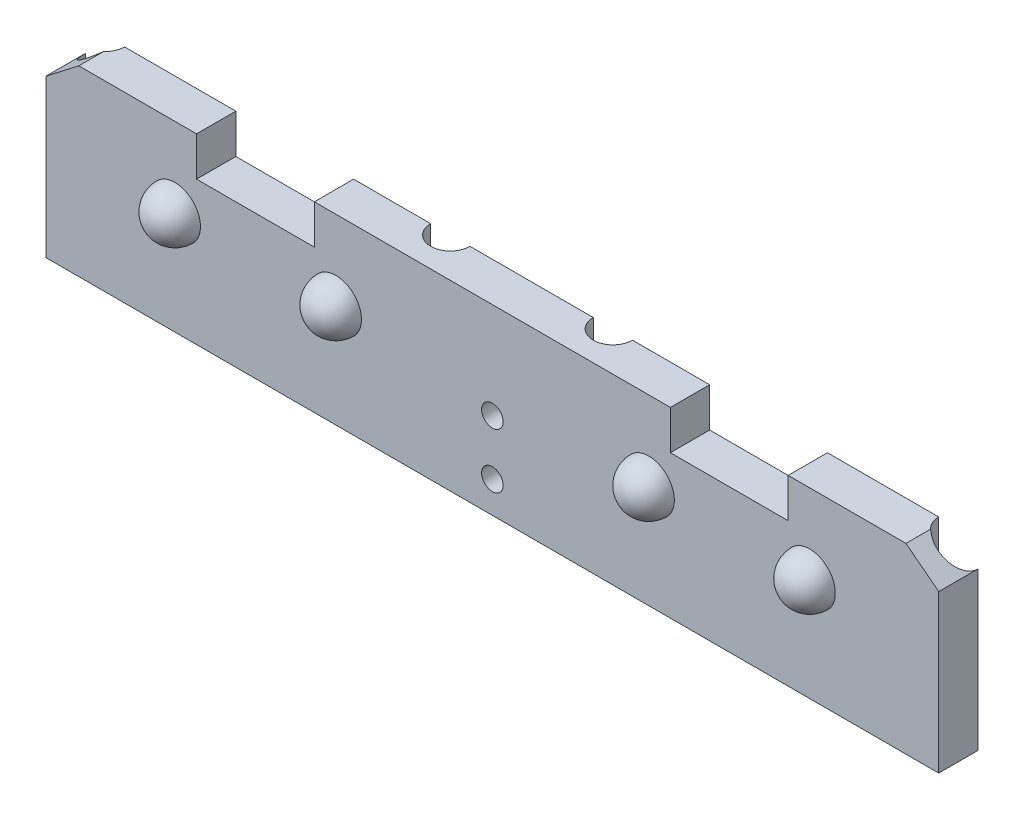
SolidWorks part; units mm, degrees
ref_plane "Front" through (0, 0, 0) normal (0, 0, 1) x (1, 0, 0)
ref_plane "Top" through (0, 0, 0) normal (0, 1, 0) x (1, 0, 0)
ref_plane "Right" through (0, 0, 0) normal (1, 0, 0) x (0, 0, -1)
sketch "Sketch1" plane through (0, 0, 0) normal (0, 0, 1) x (1, 0, 0)
  line L1 (0, 0) -> (126.7, 0)
  line L2 (0, 0) -> (0, 14)
  line L3 (0, 14) -> (126.7, 14)
  line L4 (126.7, 0) -> (126.7, 14)
  dimension "D1" = 126.7
  dimension "D2" = 14
extrude "bracketBase" add sketch "Sketch1" along normal blind 5
sketch "Sketch2" plane through (0, 0, 5) normal (0, 0, 1) x (1, 0, 0)
  line L0 (0, 0) -> (126.7, 0) construction
  line L1 (60.35, 0) -> (66.35, 0) construction
  line L2 (60.35, 0) -> (60.35, 14) construction
  line L3 (60.35, 14) -> (66.35, 14) construction
  line L4 (66.35, 0) -> (66.35, 14) construction
  line L5 (63.35, 0) -> (63.35, -7.3083) construction
  line L7 (120.7, 0) -> (126.7, 0) construction
  line L8 (120.7, 0) -> (120.7, 14) construction
  line L9 (120.7, 14) -> (126.7, 14) construction
  line L10 (126.7, 0) -> (126.7, 14) construction
  circle A0 centre (63.35, 10) radius 1.375
  circle A1 centre (63.35, 3) radius 1.375
  circle A2 centre (123.7, 10) radius 1.375
  circle A3 centre (123.7, 3) radius 1.375
  circle A4 centre (3, 3) radius 1.375
  circle A5 centre (3, 10) radius 1.375
  point P4 (63.35, 0)
  point P7 (63.35, 0)
  point P19 (63.35, 14)
  point P24 (123.7, 14)
  dimension "D3" = 2.75
  dimension "D1" = 14
  dimension "D2" = 6
  dimension "D4" = 4
  dimension "D5" = 7
extrude "mountingHoles" cut sketch "Sketch2" against normal through all both and the other way through all
sketch "distanceSensors" plane through (0, 0, 5) normal (0, 0, 1) x (1, 0, 0)
  line L0 (63.35, 0) -> (63.35, 14) construction
  line L1 (10.675, 2.25) -> (55.675, 2.25) construction
  line L2 (10.675, 2.25) -> (10.675, 22.25) construction
  line L3 (10.675, 22.25) -> (55.675, 22.25) construction
  line L4 (55.675, 2.25) -> (55.675, 22.25) construction
  line L5 (0, 0) -> (126.7, 0) construction
  line L6 (126.7, 14) -> (0, 14) construction
  line L7 (116.025, 2.25) -> (116.025, 22.25) construction
  line L8 (116.025, 2.25) -> (71.025, 2.25) construction
  line L9 (71.025, 2.25) -> (71.025, 22.25) construction
  line L10 (116.025, 22.25) -> (71.025, 22.25) construction
  circle A0 centre (63.35, 3) radius 1.375 construction
  circle A1 centre (63.35, 3) radius 1.375 construction
  circle A2 centre (19.675, 12.25) radius 9 construction
  circle A3 centre (46.675, 12.25) radius 9 construction
  circle A4 centre (80.025, 12.25) radius 9 construction
  circle A5 centre (107.025, 12.25) radius 9 construction
  point P14 (55.675, 12.25)
  dimension "D5" = 18
  dimension "D1" = 20
  dimension "D2" = 45
  dimension "D3" = 7.675
  dimension "D4" = 0.75
  dimension "D6" = 27
sketch "Sketch4" plane through (0, 0, 5) normal (0, 0, 1) x (1, 0, 0)
  line L0 (43.425, 9.0072) -> (43.425, 15.5072)
  arc A0 (43.425, 15.5072) -> (43.425, 9.0072) centre (43.425, 12.2572) ccw
  dimension "D1" = 6.5
  dimension "D2" = 0.0072
  dimension "D3" = 3.25
sketch "Sketch5" plane through (0, 0, 5) normal (0, 0, 1) x (1, 0, 0)
  line L0 (126.7, 0) -> (126.7, 14) construction
  line L1 (0, 14) -> (126.7, 14)
  line L2 (0, 14) -> (0, 22.25)
  line L3 (0, 22.25) -> (126.7, 22.25)
  line L4 (126.7, 14) -> (126.7, 22.25)
  line L5 (116.025, 22.25) -> (71.025, 22.25) construction
extrude "baseExtension" add sketch "Sketch5" against normal up to surface (5 mm away) up to face at (1.625, 3, 0)
sketch "Sketch6" plane through (0, 0, 5) normal (0, 0, 1) x (1, 0, 0)
  line L0 (33.175, 22.25) -> (33.175, 0) construction
  line L1 (10.675, 22.25) -> (55.675, 22.25) construction
  line L2 (0, 0) -> (126.7, 0) construction
  line L3 (43.425, 9.0072) -> (43.425, 15.5072) construction
  line L4 (43.425, 9.0072) -> (43.425, 15.5072) construction
  line L5 (22.925, 9.0072) -> (22.925, 15.5072)
  arc A0 (43.425, 15.5072) -> (43.425, 9.0072) centre (43.425, 12.2572) ccw construction
  arc A1 (43.425, 15.5072) -> (43.425, 9.0072) centre (43.425, 12.2572) ccw construction
  arc A2 (22.925, 15.5072) -> (22.925, 9.0072) centre (22.925, 12.2572) cw
sketch "Sketch7" plane through (0, 0, 5) normal (0, 0, 1) x (1, 0, 0)
  line L0 (43.425, 9.0072) -> (43.425, 15.5072) construction
  line L1 (43.425, 9.0072) -> (43.425, 15.5072) construction
  line L2 (63.35, 0) -> (63.35, 22.25) construction
  line L3 (126.7, 22.25) -> (0, 22.25) construction
  line L4 (83.275, 9.0072) -> (83.275, 15.5072)
  arc A0 (43.425, 15.5072) -> (43.425, 9.0072) centre (43.425, 12.2572) ccw construction
  arc A1 (43.425, 15.5072) -> (43.425, 9.0072) centre (43.425, 12.2572) ccw construction
  arc A2 (83.275, 15.5072) -> (83.275, 9.0072) centre (83.275, 12.2572) cw
sketch "Sketch8" plane through (0, 0, 5) normal (0, 0, 1) x (1, 0, 0)
  line L0 (63.35, 0) -> (63.35, 22.25) construction
  line L1 (0, 0) -> (126.7, 0) construction
  line L2 (22.925, 9.0072) -> (22.925, 15.5072) construction
  line L3 (22.925, 9.0072) -> (22.925, 15.5072) construction
  line L4 (103.775, 9.0072) -> (103.775, 15.5072)
  arc A0 (22.925, 9.0072) -> (22.925, 15.5072) centre (22.925, 12.2572) ccw construction
  arc A1 (22.925, 9.0072) -> (22.925, 15.5072) centre (22.925, 12.2572) ccw construction
  arc A2 (103.775, 9.0072) -> (103.775, 15.5072) centre (103.775, 12.2572) cw
revolve "Revolve1" add sketch "Sketch4" angle 180 about L0
revolve "Revolve2" add sketch "Sketch6" angle 180 about L5
revolve "Revolve3" add sketch "Sketch7" angle 180 about L4
revolve "Revolve4" add sketch "Sketch8" angle 180 about L4
sketch "Sketch9" plane through (0, 0, 5) normal (0, 0, 1) x (1, 0, 0)
  line L0 (10.675, 22.25) -> (55.675, 22.25) construction
  line L1 (25.675, 22.25) -> (40.675, 22.25)
  line L2 (25.675, 22.25) -> (25.675, 17.25)
  line L3 (25.675, 17.25) -> (40.675, 17.25)
  line L4 (40.675, 22.25) -> (40.675, 17.25)
  line L5 (63.35, 14) -> (63.35, 22.25) construction
  line L6 (126.7, 22.25) -> (0, 22.25) construction
  line L7 (101.025, 17.25) -> (86.025, 17.25)
  line L8 (86.025, 22.25) -> (86.025, 17.25)
  line L9 (101.025, 22.25) -> (86.025, 22.25)
  line L10 (101.025, 22.25) -> (101.025, 17.25)
  point P7 (33.175, 22.25)
  point P8 (33.175, 22.25)
  dimension "D1" = 15
  dimension "D2" = 5
extrude "Cut-Extrude2" cut sketch "Sketch9" against normal through all both and the other way through all
sketch "Sketch10" plane through (0, 0, 5) normal (0, 0, 1) x (1, 0, 0)
  line L0 (116.025, 22.25) -> (126.7, 14)
  line L3 (126.7, 14) -> (126.7, 22.25)
  line L4 (126.7, 22.25) -> (116.025, 22.25)
  line L5 (63.35, 14) -> (63.35, 22.25) construction
  line L6 (86.025, 22.25) -> (40.675, 22.25) construction
  line L7 (0, 14) -> (0, 22.25)
  line L8 (10.675, 22.25) -> (0, 14)
  line L9 (0, 22.25) -> (10.675, 22.25)
extrude "Cut-Extrude3" cut sketch "Sketch10" against normal through all both and the other way through all
sketch "Sketch11" plane through (0, 0, 0) normal (0, -1, 0) x (1, 0, 0)
  line L2 (126.7, 5) -> (126.7, 0) construction
  line L3 (63.35, 0) -> (63.35, 5) construction
  line L4 (0, 0) -> (126.7, 0) construction
  line L5 (0, 5) -> (126.7, 5) construction
  circle A1 centre (126.95, 1.1558) radius 2.5
  circle A2 centre (-0.25, 1.1558) radius 2.5
  dimension "D1" = 5
  dimension "D2" = 0.25
  dimension "D3" = 1.1825
extrude "Cut-Extrude4" cut sketch "Sketch11" against normal through all
sketch "Sketch12" plane through (0, 0, 0) normal (0, -1, 0) x (1, 0, 0)
  line L1 (1.9668, 0) -> (124.7332, 0) construction
  line L2 (63.35, 5) -> (63.35, 0) construction
  line L3 (0, 5) -> (126.7, 5) construction
  circle A0 centre (117.7, 0) radius 2.5
  circle A1 centre (73.7, 0) radius 2.5
  circle A3 centre (53, 0) radius 2.5
  circle A4 centre (9, 0) radius 2.5
  dimension "D1" = 5
  dimension "D2" = 9
  dimension "D3" = 44
extrude "Cut-Extrude5" cut sketch "Sketch12" against normal through all
sketch "Sketch13" plane through (0, 0, 0) normal (0, -1, 0) x (1, 0, 0)
  line L0 (63.35, 5) -> (63.35, 0) construction
  line L1 (0, 5) -> (126.7, 5) construction
  line L2 (55.5, 0) -> (71.2, 0) construction
  line L3 (120.2, 0) -> (124.7332, 0) construction
  line L4 (126.7, 5) -> (120.2, 5)
  line L5 (126.7, 5) -> (126.7, 0)
  line L6 (126.7, 0) -> (120.2, 0)
  line L7 (120.2, 5) -> (120.2, 0)
  line L8 (0, 0) -> (6.5, 0)
  line L9 (6.5, 5) -> (6.5, 0)
  line L10 (0, 5) -> (6.5, 5)
  line L11 (0, 5) -> (0, 0)
  dimension "D1" = 6.5
extrude "Cut-Extrude6" cut sketch "Sketch13" against normal through all both and the other way through all
sketch "Sketch14" plane through (0, 0, 0) normal (0, -1, 0) x (1, 0, 0)
  line L6 (120.2, 0) -> (120.2, 5)
  line L7 (120.2, 5) -> (6.5, 5)
  line L8 (6.5, 5) -> (6.5, 0)
  line L9 (11.5, 0) -> (50.5, 0)
  line L10 (55.5, 0) -> (71.2, 0)
  line L11 (76.2, 0) -> (115.2, 0)
  line L12 (120.2, 0) -> (120.2, 5)
  line L13 (120.2, 5) -> (6.5, 5)
  line L14 (6.5, 5) -> (6.5, 0)
  line L15 (11.5, 0) -> (50.5, 0)
  line L16 (55.5, 0) -> (71.2, 0)
  line L17 (76.2, 0) -> (115.2, 0)
  arc A4 (120.2, 0) -> (115.2, 0) centre (117.7, 0) ccw
  arc A5 (11.5, 0) -> (6.5, 0) centre (9, 0) ccw
  arc A6 (55.5, 0) -> (50.5, 0) centre (53, 0) ccw
  arc A7 (76.2, 0) -> (71.2, 0) centre (73.7, 0) ccw
  arc A8 (120.2, 0) -> (115.2, 0) centre (117.7, 0) ccw
  arc A9 (11.5, 0) -> (6.5, 0) centre (9, 0) ccw
  arc A10 (55.5, 0) -> (50.5, 0) centre (53, 0) ccw
  arc A11 (76.2, 0) -> (71.2, 0) centre (73.7, 0) ccw
  dimension "D1" = 0
extrude "Boss-Extrude1" add sketch "Sketch14" along normal blind 1
